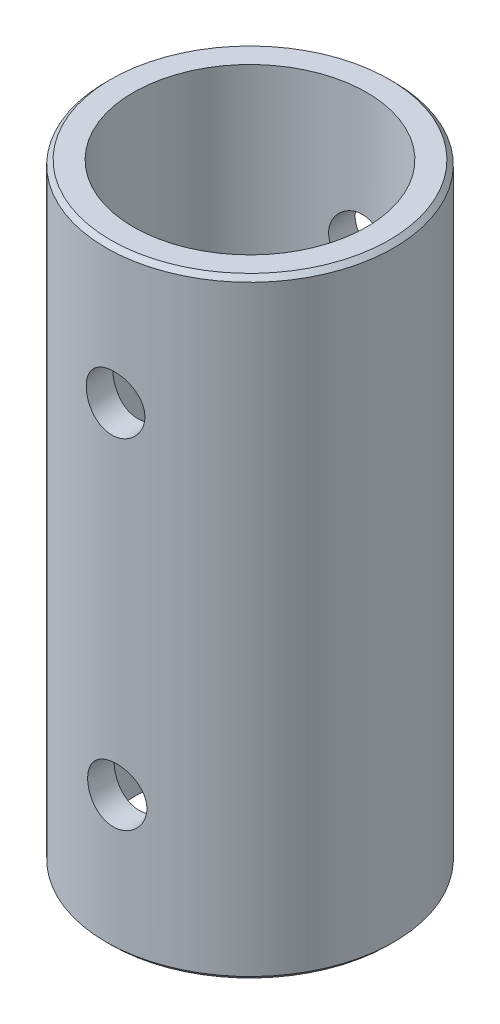
SolidWorks part; units mm, degrees
ref_plane "Front Plane" through (0, 0, 0) normal (0, 0, 1) x (1, 0, 0)
ref_plane "Top Plane" through (0, 0, 0) normal (0, 1, 0) x (1, 0, 0)
ref_plane "Right Plane" through (0, 0, 0) normal (1, 0, 0) x (0, 0, -1)
sketch "Sketch1" plane through (0, 0, 0) normal (0, 1, 0) x (1, 0, 0)
  circle A0 centre (0, 0) radius 7.94
  circle A1 centre (0, 0) radius 6.44
  dimension "D1" = 15.88
  dimension "D2" = 1.5
extrude "Boss-Extrude1" add sketch "Sketch1" along normal blind 33.7
chamfer "Chamfer1" distance 0.25 angle 45 2 edges at (0, 0, 7.94) (0, 33.7, 7.94)
sketch "Sketch2" plane through (0.2669, 0, 5.8439) normal (0.0456, 0, 0.999) x (0.999, 0, -0.0456)
  circle A0 centre (0, 26.2) radius 1.55 construction
  circle A1 centre (0, 26.2) radius 1.55
  ellipse E0 centre (0.0902, 7.5) end of major axis (0.0902, 9.05) minor radius 1.5498 construction
  ellipse E1 centre (0.0902, 7.5) end of major axis (0.0902, 9.05) minor radius 1.5498
extrude "Cut-Extrude1" cut sketch "Sketch2" against normal through all both and the other way through all
